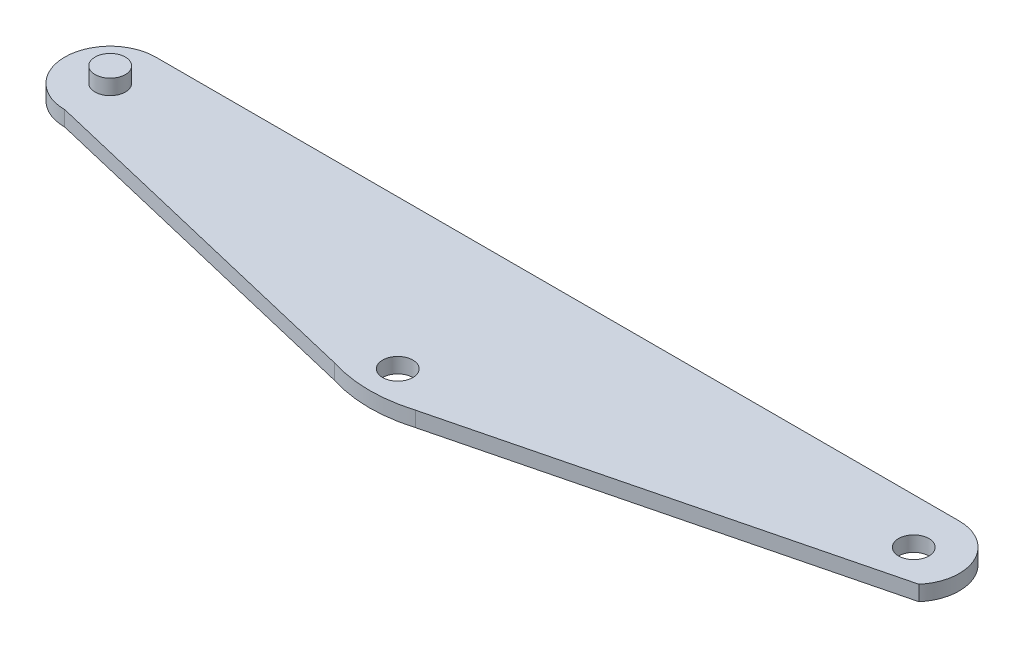
SolidWorks part; units mm, degrees
ref_plane "Front Plane" through (0, 0, 0) normal (0, 0, 1) x (1, 0, 0)
ref_plane "Top Plane" through (0, 0, 0) normal (0, 1, 0) x (1, 0, 0)
ref_plane "Right Plane" through (0, 0, 0) normal (1, 0, 0) x (0, 0, -1)
sketch "Sketch1" plane through (0, 0, 0) normal (0, 1, 0) x (1, 0, 0)
  line L0 (-26.5, 0) -> (26.5, 0) construction
  line L1 (-26.5, 3) -> (26.5, 3)
  line L2 (28.7867, -1.9419) -> (2.2479, -8.5981)
  line L3 (-26.5, -3) -> (-3.1539, -8.5641)
  circle A0 centre (-26.5, 0) radius 1
  circle A1 centre (26.5, 0) radius 1
  circle A2 centre (-0.7096, -6.8247) radius 1
  arc A3 (-26.5, 3) -> (-26.5, -3) centre (-26.5, 0) ccw
  arc A6 (-3.1539, -8.5641) -> (2.2479, -8.5981) centre (-0.3984, 0.1093) ccw
  arc A7 (28.7867, -1.9419) -> (26.5, 3) centre (26.5, 0) ccw
  point P3 (0, 0)
  point P14 (-1.1708, -6.3315)
  point P17 (-0.7096, -6.8247)
  dimension "D2" = 2
  dimension "D3" = 2
  dimension "D5" = 2
  dimension "D1" = 53
  dimension "D4" = 3
  dimension "D6" = 24
  dimension "D8" = 3
  dimension "D9" = 3
extrude "Boss-Extrude1" add sketch "Sketch1" along normal blind 1
sketch "Sketch2" plane through (0, 1, 0) normal (0, 1, 0) x (1, 0, 0)
  circle A0 centre (-26.5, 0) radius 1
extrude "Boss-Extrude2" add sketch "Sketch2" along normal blind 1
sketch "Sketch3" plane through (0, 0, 0) normal (0, -1, 0) x (1, 0, 0)
  circle A0 centre (-26.5, 0) radius 1
extrude "Boss-Extrude3" add sketch "Sketch3" against normal blind 1
